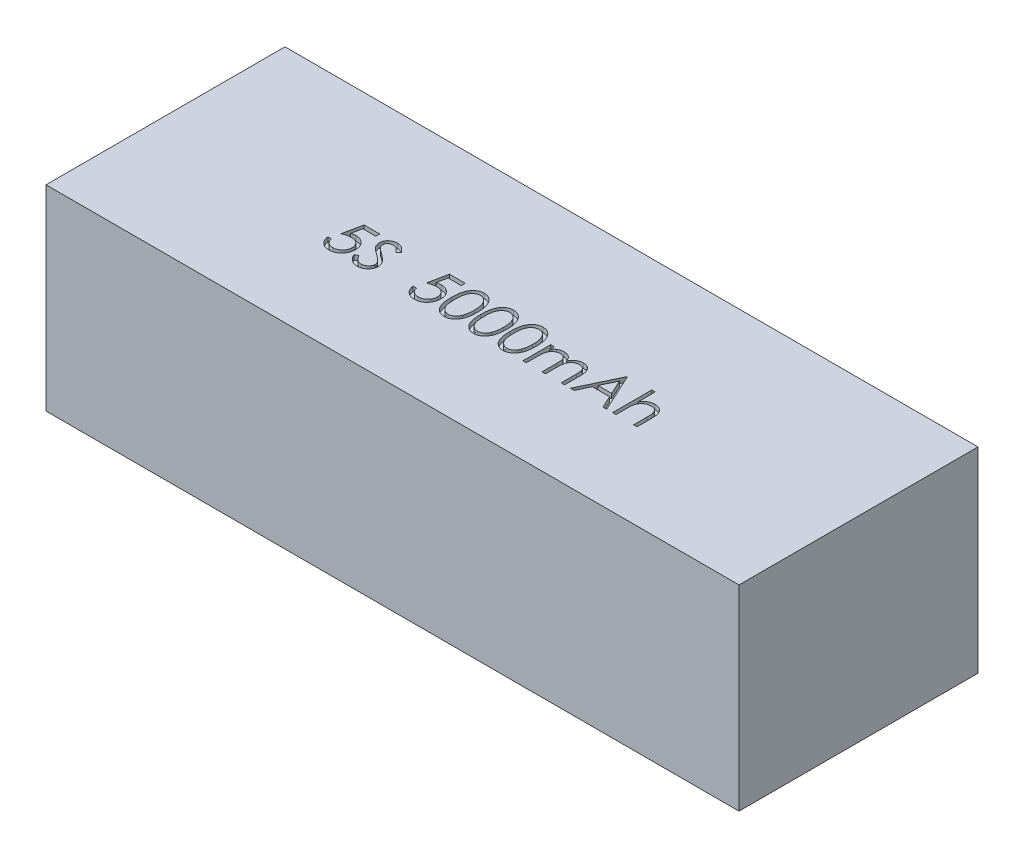
SolidWorks part; units mm, degrees
ref_plane "Front Plane" through (0, 0, 0) normal (0, 0, 1) x (1, 0, 0)
ref_plane "Top Plane" through (0, 0, 0) normal (0, 1, 0) x (1, 0, 0)
ref_plane "Right Plane" through (0, 0, 0) normal (1, 0, 0) x (0, 0, -1)
sketch "Sketch1" plane through (0, 0, 0) normal (0, 1, 0) x (1, 0, 0)
  line L1 (0, 0) -> (145, 0)
  line L2 (0, 0) -> (0, 50)
  line L3 (0, 50) -> (145, 50)
  line L4 (145, 0) -> (145, 50)
  dimension "D1" = 145
  dimension "D2" = 50
extrude "Boss-Extrude1" add sketch "Sketch1" along normal blind 41
sketch "Sketch2" plane through (0, 41, 0) normal (0, 1, 0) x (1, 0, 0)
  line L0 (0, 18) -> (145, 18) construction
  line L1 (0, 50) -> (0, 0) construction
  line L2 (145, 0) -> (145, 50) construction
  line L3 (0, 0) -> (145, 0) construction
  text T0 "5S  5000mAh" font "Century Gothic" height 8
  dimension "D1" = 18
extrude "Cut-Extrude1" cut sketch "Sketch2" against normal blind 1
